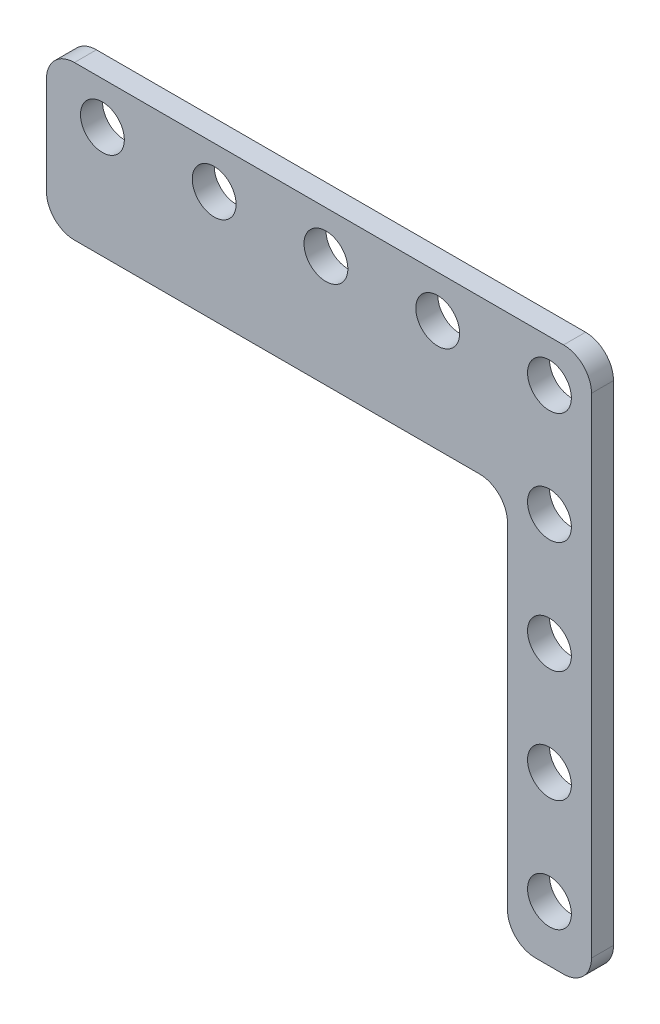
SolidWorks part; units mm, degrees
ref_plane "Front Plane" through (0, 0, 0) normal (0, 0, 1) x (1, 0, 0)
ref_plane "Top Plane" through (0, 0, 0) normal (0, 1, 0) x (1, 0, 0)
ref_plane "Right Plane" through (0, 0, 0) normal (1, 0, 0) x (0, 0, -1)
sketch "Sketch1" plane through (0, 0, 0) normal (0, 0, 1) x (1, 0, 0)
  line L0 (-1.6002, -57.15) -> (1.6002, -57.15)
  line L1 (4.7752, -53.975) -> (4.7752, 1.6002)
  line L2 (1.6002, 4.7752) -> (-53.975, 4.7752)
  line L3 (-57.15, 1.6002) -> (-57.15, -9.525)
  line L4 (-53.975, -12.7) -> (-7.9502, -12.7)
  line L5 (-4.7752, -15.875) -> (-4.7752, -53.975)
  circle A0 centre (-12.7, 0) radius 2.4892
  circle A1 centre (0, 0) radius 2.4892
  circle A2 centre (-25.4, 0) radius 2.4892
  circle A3 centre (-38.1, 0) radius 2.4892
  circle A4 centre (-50.8, 0) radius 2.4892
  circle A5 centre (-12.7, -12.7) radius 2.4892 [skipped]
  circle A6 centre (-25.4, -12.7) radius 2.4892 [skipped]
  circle A7 centre (-38.1, -12.7) radius 2.4892 [skipped]
  circle A8 centre (-50.8, -12.7) radius 2.4892 [skipped]
  arc A9 (-4.7752, -53.975) -> (-1.6002, -57.15) centre (-1.6002, -53.975) ccw
  arc A10 (1.6002, -57.15) -> (4.7752, -53.975) centre (1.6002, -53.975) ccw
  arc A11 (4.7752, 1.6002) -> (1.6002, 4.7752) centre (1.6002, 1.6002) ccw
  arc A12 (-53.975, 4.7752) -> (-57.15, 1.6002) centre (-53.975, 1.6002) ccw
  arc A13 (-57.15, -9.525) -> (-53.975, -12.7) centre (-53.975, -9.525) ccw
  arc A14 (-7.9502, -12.7) -> (-4.7752, -15.875) centre (-7.9502, -15.875) cw
  circle A15 centre (-12.7, -25.4) radius 2.4892 [skipped]
  circle A16 centre (-25.4, -25.4) radius 2.4892 [skipped]
  circle A17 centre (-38.1, -25.4) radius 2.4892 [skipped]
  circle A18 centre (-50.8, -25.4) radius 2.4892 [skipped]
  circle A19 centre (-12.7, -38.1) radius 2.4892 [skipped]
  circle A20 centre (-25.4, -38.1) radius 2.4892 [skipped]
  circle A21 centre (-38.1, -38.1) radius 2.4892 [skipped]
  circle A22 centre (-50.8, -38.1) radius 2.4892 [skipped]
  circle A23 centre (-12.7, -50.8) radius 2.4892 [skipped]
  circle A24 centre (-25.4, -50.8) radius 2.4892 [skipped]
  circle A25 centre (-38.1, -50.8) radius 2.4892 [skipped]
  circle A26 centre (-50.8, -50.8) radius 2.4892 [skipped]
  circle A27 centre (0, -12.7) radius 2.4892
  circle A28 centre (0, -25.4) radius 2.4892
  circle A29 centre (0, -38.1) radius 2.4892
  circle A30 centre (0, -50.8) radius 2.4892
  point P0 (-38.1, 0)
  dimension "D9" = 3.175
  dimension "D12" = 4.9784
  dimension "D1" = 4.7752
  dimension "D2" = 4.7752
  dimension "D5" = 6.35
  dimension "D6" = 6.35
  dimension "D7" = 61.9252
  dimension "D8" = 61.9252
  dimension "D10" = 17.4752
  dimension "D11" = 9.5504
  dimension "D3" = 5
  dimension "D4" = 5
extrude "Boss-Extrude1" add sketch "Sketch1" against normal blind 2.5
